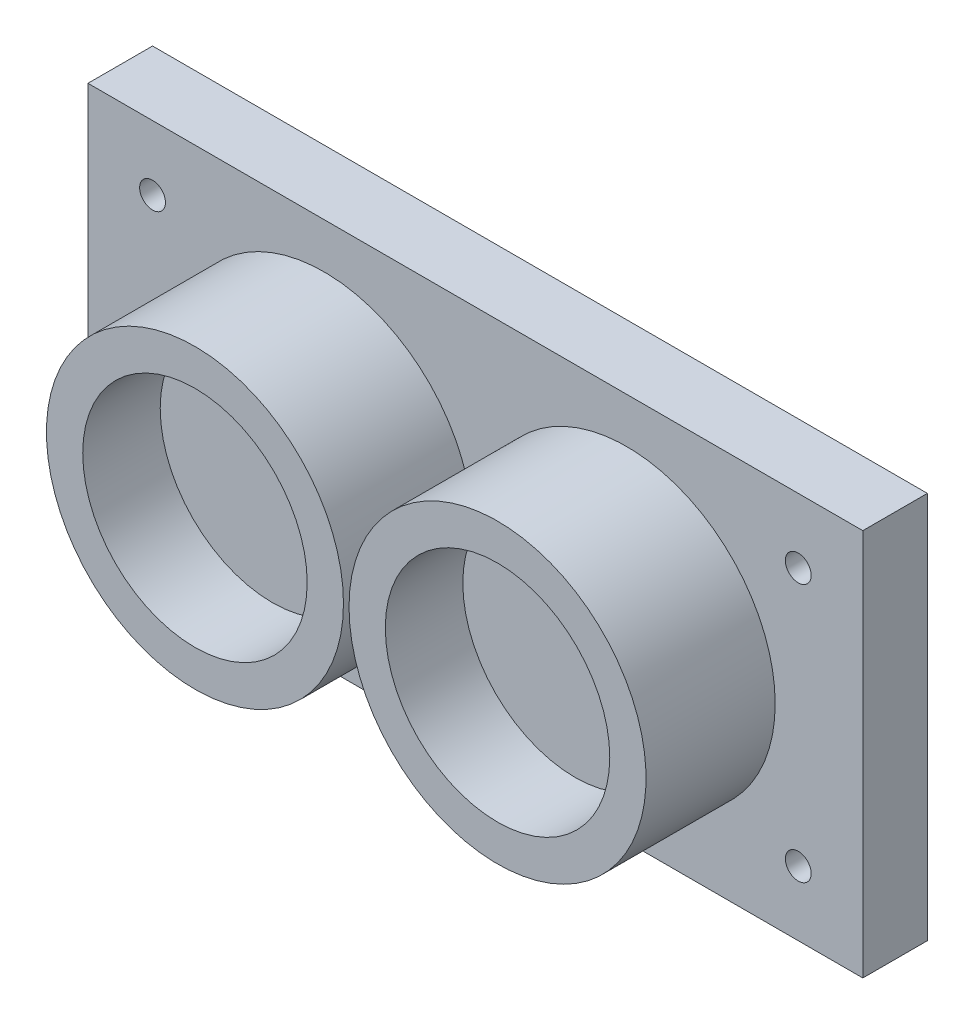
SolidWorks part; units mm, degrees
ref_plane "Front Plane" through (0, 0, 0) normal (0, 0, 1) x (1, 0, 0)
ref_plane "Top Plane" through (0, 0, 0) normal (0, 1, 0) x (1, 0, 0)
ref_plane "Right Plane" through (0, 0, 0) normal (1, 0, 0) x (0, 0, -1)
sketch "Sketch1" plane through (0, 0, 0) normal (0, 0, 1) x (1, 0, 0)
  line L1 (30, -15) -> (-30, -15)
  line L2 (30, -15) -> (30, 15)
  line L3 (30, 15) -> (-30, 15)
  line L4 (-30, -15) -> (-30, 15)
  line L5 (30, -15) -> (-30, 15) construction
  line L6 (30, 15) -> (-30, -15) construction
  point P0 (0, 0)
  dimension "D1" = 30
  dimension "D2" = 60
extrude "Boss-Extrude2" add sketch "Sketch1" along normal blind 5
sketch "Sketch2" plane through (0, 0, 5) normal (0, 0, 1) x (1, 0, 0)
  line L0 (0, 24.6609) -> (0, -25.1816) construction
  circle A0 centre (-11.715, 0) radius 11.5
  circle A1 centre (11.715, 0) radius 11.5
  dimension "D1" = 23
  dimension "D2" = 23.43
extrude "Boss-Extrude3" add sketch "Sketch2" along normal blind 10 contours A0 | A1
sketch "Sketch3" plane through (0, 0, 15) normal (0, 0, 1) x (1, 0, 0)
  circle A2 centre (-11.715, 0) radius 8.69
  circle A3 centre (-11.715, 0) radius 8.69
  circle A5 centre (11.715, 0) radius 8.69
  circle A6 centre (11.715, 0) radius 8.69
  dimension "D2" = 2.81
  dimension "D1" = 2.81
extrude "Cut-Extrude2" cut sketch "Sketch3" against normal blind 6
sketch "Sketch4" plane through (0, 0, 5) normal (0, 0, 1) x (1, 0, 0)
  line L0 (30, 15) -> (-30, 15) construction
  line L1 (-30, 15) -> (-30, -15) construction
  line L2 (0, 22.3154) -> (0, -17.1859) construction
  line L3 (-35.4774, 0) -> (34.8288, 0) construction
  circle A0 centre (-25, 10) radius 1
  circle A1 centre (25, 10) radius 1
  circle A2 centre (25, -10) radius 1
  circle A3 centre (-25, -10) radius 1
  dimension "D3" = 2
  dimension "D1" = 5
  dimension "D2" = 5
sketch "Sketch5" plane through (0, 0, 5) normal (0, 0, 1) x (1, 0, 0)
sketch "Sketch6" plane through (0, 0, 5) normal (0, 0, 1) x (1, 0, 0)
  line L0 (0, 21.5364) -> (0, -19.4535) construction
  line L1 (-37.2703, 0) -> (45.6022, 0) construction
extrude "Cut-Extrude4" cut sketch "Sketch4" against normal blind 10 contours A2 | A1 | A0 | A3
